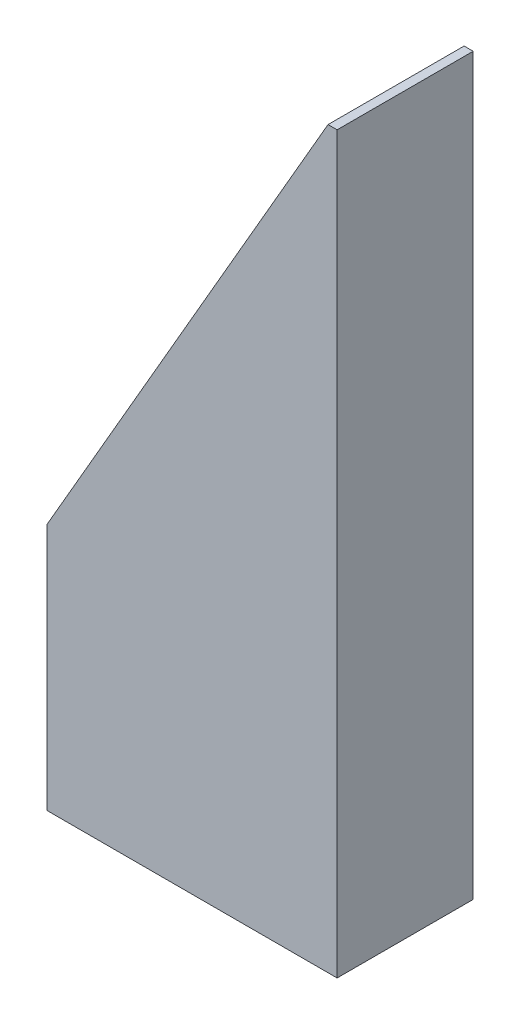
SolidWorks part; units mm, degrees
ref_plane "Front Plane" through (0, 0, 0) normal (0, 0, 1) x (1, 0, 0)
ref_plane "Top Plane" through (0, 0, 0) normal (0, 1, 0) x (1, 0, 0)
ref_plane "Right Plane" through (0, 0, 0) normal (1, 0, 0) x (0, 0, -1)
sketch "Sketch1" plane through (0, 0, 0) normal (0, 0, 1) x (1, 0, 0)
  line L0 (0, 27.2764) -> (31, 80.97)
  line L1 (0, 0) -> (32, 0)
  line L2 (0, 0) -> (0, 27.2764)
  line L3 (31, 80.97) -> (32, 80.97)
  line L4 (32, 0) -> (32, 80.97)
  dimension "D1" = 32
  dimension "D2" = 80.97
  dimension "D3" = 30
  dimension "D4" = 1
extrude "Boss-Extrude1" add sketch "Sketch1" along normal blind 15
